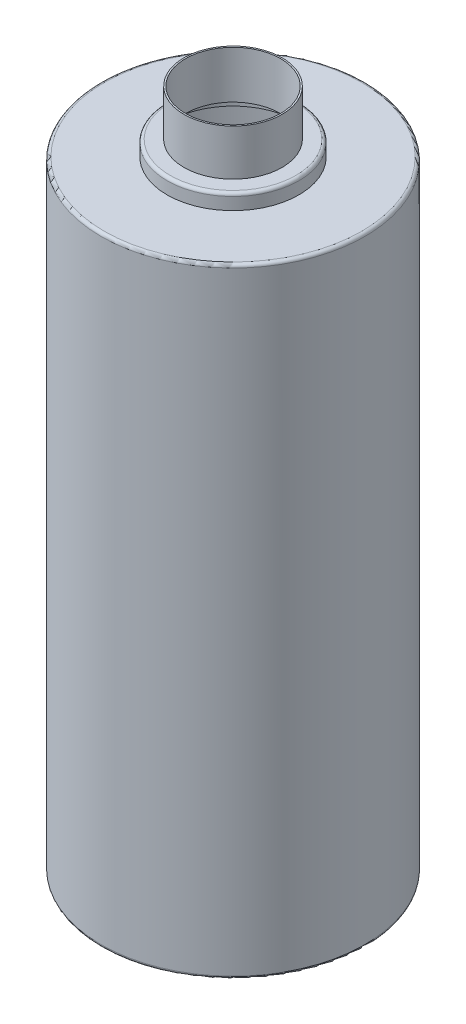
SolidWorks part; units mm, degrees
ref_plane "前视基准面" through (0, 0, 0) normal (0, 0, 1) x (1, 0, 0)
ref_plane "上视基准面" through (0, 0, 0) normal (0, 1, 0) x (1, 0, 0)
ref_plane "右视基准面" through (0, 0, 0) normal (1, 0, 0) x (0, 0, -1)
sketch "草图2" plane through (0, 0, 0) normal (0, 0, 1) x (1, 0, 0)
  line L0 (0, 36.9395) -> (0, -40.9831) construction
  line L1 (0, 111) -> (16, 111)
  line L4 (43, 91) -> (43, -111)
  line L5 (43, -111) -> (0, -111)
  line L6 (0, -111) -> (0, 111)
  line L7 (16, 111) -> (16, 96)
  line L8 (16, 96) -> (21.5, 96)
  line L9 (21.5, 96) -> (21.5, 91)
  line L10 (21.5, 91) -> (43, 91)
  dimension "D1" = 16
  dimension "D2" = 21.5
  dimension "D3" = 43
  dimension "D4" = 15
  dimension "D5" = 5
  dimension "D6" = 222
  dimension "D7" = 111
revolve "旋转1" add sketch "草图2" angle 360 about L0
fillet "圆角1" radius 1 3 edges at (0, -111, 43) (0, 96, 21.5) (0, 91, 43)
shell "抽壳1" thickness 0.5
